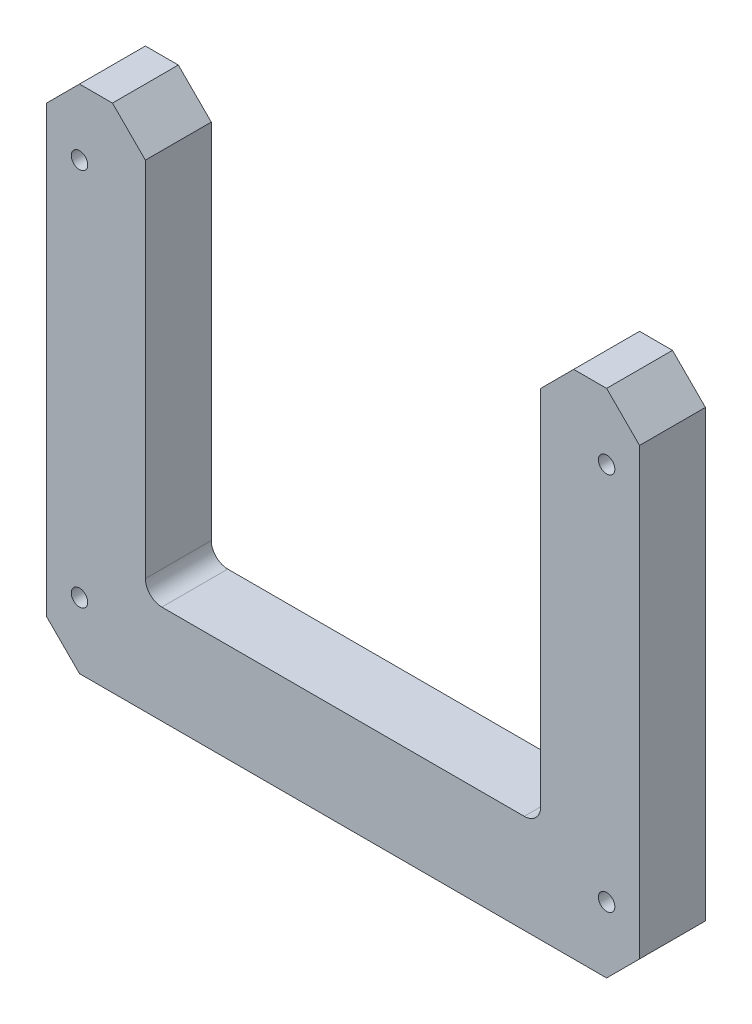
SolidWorks part; units mm, degrees
material "Beech"
ref_plane "Front Plane" through (0, 0, 0) normal (0, 0, 1) x (1, 0, 0)
ref_plane "Top Plane" through (0, 0, 0) normal (0, 1, 0) x (1, 0, 0)
ref_plane "Right Plane" through (0, 0, 0) normal (1, 0, 0) x (0, 0, -1)
sketch "Sketch1" plane through (0, 0, 0) normal (0, 0, 1) x (1, 0, 0)
  line L1 (-237.3775, 69.0432) -> (-237.3775, -16.6818) construction
  line L2 (-231.0275, 69.0432) -> (-231.0275, -10.3318)
  line L3 (-148.4775, 69.0432) -> (-148.4775, -16.6818) construction
  line L4 (-237.3775, -16.6818) -> (-148.4775, -16.6818) construction
  line L5 (-234.2025, -16.6818) -> (-151.6525, -16.6818) construction
  line L6 (-231.0275, -10.3318) -> (-154.8275, -10.3318)
  line L7 (-154.8275, 69.0432) -> (-154.8275, -10.3318)
  line L8 (-250.0775, 69.0432) -> (-250.0775, -29.3818)
  line L13 (-250.0775, -29.3818) -> (-135.7775, -29.3818)
  line L14 (-135.7775, 69.0432) -> (-135.7775, -29.3818)
  line L15 (-250.0775, 69.0432) -> (-231.0275, 69.0432)
  line L16 (-154.8275, 69.0432) -> (-135.7775, 69.0432)
  dimension "D1" = 6.35
  dimension "D2" = 12.7
extrude "Boss-Extrude1" add sketch "Sketch1" along normal blind 12.7
fillet "Fillet1" radius 3.175 2 edges at (-154.8275, -10.3318, 6.35) (-231.0275, -10.3318, 6.35)
chamfer "Chamfer1" distance 6.35 angle 45 6 edges at (-250.0775, -29.3818, 6.35) (-135.7775, -29.3818, 6.35) (-135.7775, 69.0432, 6.35) (-154.8275, 69.0432, 6.35) (-250.0775, 69.0432, 6.35) (-231.0275, 69.0432, 6.35)
hole_wizard "Hole1" positions "Sketch2" profile "Sketch3" legacy
sketch "Sketch2" plane through (-124.0045, -215.2871, -12.7) normal (0, 0, -1) x (-1, 0, 0)
  line L1 (0, 465.9538) -> (0, 167.7243) construction
  line L2 (126.073, 235.1179) -> (113.373, 235.1179) construction
  line L6 (119.723, 284.3304) -> (119.723, 185.9054) construction
  line L10 (68.923, 285.9179) -> (68.923, 200.1929) construction
  point P1 (113.65, 128.8076)
  point P3 (113.65, 23.941)
  point P5 (-94.6, 161.3743)
  point P7 (94.6, 161.3743)
  point P9 (0, 161.3743)
  point P11 (0, 193.1243)
  point P13 (0, 440.5538)
  point P15 (0, 301.9704)
  point P17 (40.9792, 301.9704)
  point P19 (166.7958, 301.9704)
  point P21 (207.775, 440.5538)
  point P23 (207.775, 333.0214)
  point P25 (207.775, 225.489)
  point P27 (207.775, 137.4243)
  point P29 (207.775, 10.4243)
  point P33 (-207.775, 10.4243)
  point P34 (-207.775, 137.4243)
  point P35 (-207.775, 225.489)
  point P36 (-207.775, 333.0214)
  point P37 (-207.775, 440.5538)
  point P38 (-166.7958, 301.9704)
  point P39 (-40.9792, 301.9704)
  point P40 (-113.65, 23.941)
  point P41 (-113.65, 128.8076)
  point P65 (119.723, 198.6054)
  point P68 (119.723, 271.6304)
  point P78 (18.123, 198.6054)
  point P79 (18.123, 271.6304)
sketch "Sketch3" plane through (-237.6545, -86.4795, -12.7) normal (1, 0, 0) x (0, 1, 0)
  line L0 (0, 0) -> (0, 32.7039)
  line L1 (0, 32.7039) -> (1.5875, 31.75)
  line L2 (1.5875, 31.75) -> (1.5875, 4.0177)
  line L3 (1.5875, 4.0177) -> (5.08, 0)
  line L4 (5.08, 0) -> (0, 0)
  line L5 (0, -14.3089) -> (0, 102.4216) construction
  line L6 (0, 32.7039) -> (-1.5875, 31.75) construction
  line L7 (-1.5875, 4.0177) -> (-5.08, 0) construction
  dimension "Diameter" = 3.175
  dimension "Depth" = 31.75
  dimension "C-Sink Diameter" = 10.16
  dimension "C-Sink Angle" = 82
  dimension "Drill Angle" = 118
